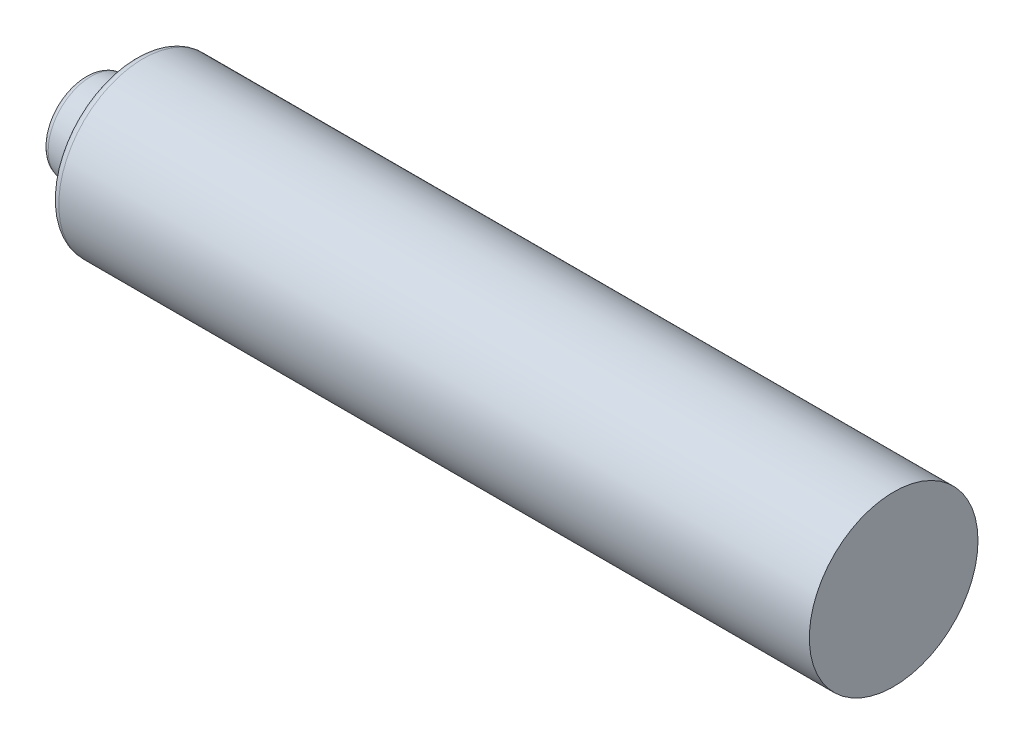
SolidWorks part; units mm, degrees
ref_plane "Front Plane" through (0, 0, 0) normal (0, 0, 1) x (1, 0, 0)
ref_plane "Top Plane" through (0, 0, 0) normal (0, 1, 0) x (1, 0, 0)
ref_plane "Right Plane" through (0, 0, 0) normal (1, 0, 0) x (0, 0, -1)
sketch "Sketch1" plane through (0, 0, 0) normal (1, 0, 0) x (0, 0, -1)
  circle A0 centre (0, 0) radius 5
  dimension "D1" = 10
extrude "Boss-Extrude1" add sketch "Sketch1" along normal blind 45
sketch "Sketch2" plane through (0, 0, 0) normal (-1, 0, 0) x (0, 0, 1)
  circle A2 centre (0, 0) radius 3
  circle A3 centre (0, 0) radius 3
  dimension "D1" = 2
extrude "Boss-Extrude2" add sketch "Sketch2" along normal blind 3 draft 10
fillet "Fillet1" radius 0.5 2 edges at (-3, 0, 2.471) (0, 0, -5)
